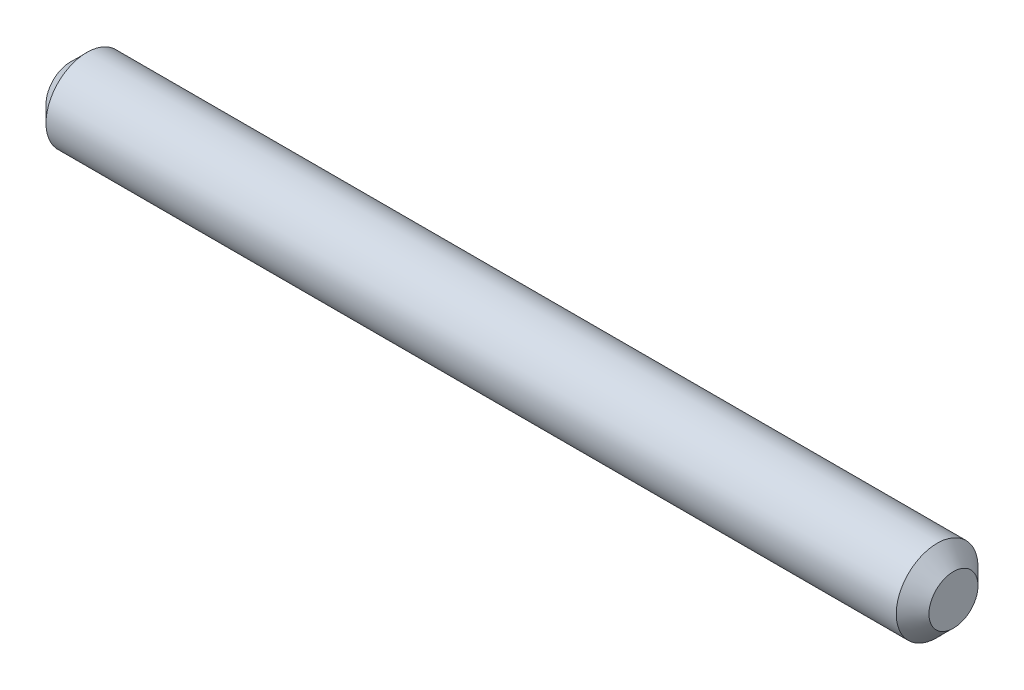
SolidWorks part; units mm, degrees
ref_plane "Front Plane" through (0, 0, 0) normal (0, 0, 1) x (1, 0, 0)
ref_plane "Top Plane" through (0, 0, 0) normal (0, 1, 0) x (1, 0, 0)
ref_plane "Right Plane" through (0, 0, 0) normal (1, 0, 0) x (0, 0, -1)
sketch "Sketch1" plane through (0, 0, 0) normal (0, 0, 1) x (1, 0, 0)
  line L0 (-29.9169, 0) -> (24.0831, 0) construction
  line L1 (-29.9169, 0) -> (-29.9169, 2.5)
  line L2 (-29.9169, 2.5) -> (24.0831, 2.5)
  line L3 (24.0831, 2.5) -> (24.0831, 0)
  line L4 (-29.9169, 0) -> (24.0831, 0)
  dimension "D1" = 54
  dimension "D2" = 2.5
revolve "Revolve1" add sketch "Sketch1" angle 360 about L0
chamfer "Chamfer1" distance 1 angle 45 2 edges at (-29.9169, 0, 2.5) (24.0831, 0, 2.5)
